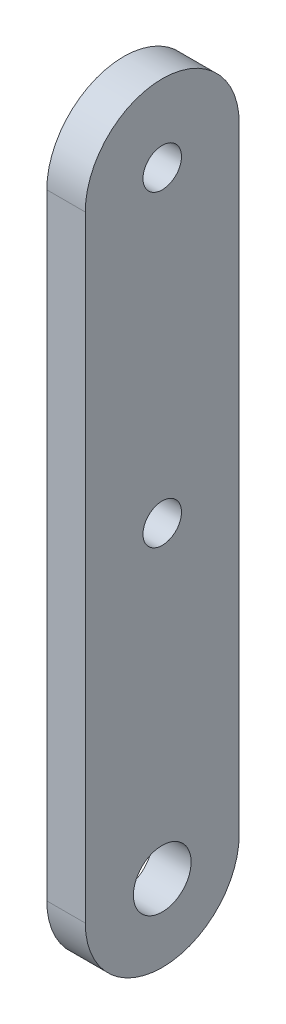
SolidWorks part; units mm, degrees
material "6061-T6 (SS)"
ref_plane "Front Plane" through (0, 0, 0) normal (0, 0, 1) x (1, 0, 0)
ref_plane "Top Plane" through (0, 0, 0) normal (0, 1, 0) x (1, 0, 0)
ref_plane "Right Plane" through (0, 0, 0) normal (1, 0, 0) x (0, 0, -1)
sketch "Sketch1" plane through (0, 0, 0) normal (1, 0, 0) x (0, 0, -1)
  line L0 (0, 50.8) -> (0, 0) construction
  line L3 (0, 0) -> (0, -50.8) construction
  line L4 (12.7, 50.8) -> (12.7, -50.8)
  line L5 (-12.7, 50.8) -> (-12.7, -50.8)
  arc A0 (12.7, 50.8) -> (-12.7, 50.8) centre (0, 50.8) ccw
  arc A3 (-12.7, -50.8) -> (12.7, -50.8) centre (0, -50.8) ccw
  circle A4 centre (0, 50.8) radius 3.175
  circle A5 centre (0, 0) radius 3.175
  circle A6 centre (0, -50.8) radius 4.7625
  point P3 (0, 15.1395)
  point P10 (0, -17.7431)
  dimension "D1" = 6.35
  dimension "D2" = 9.525
  dimension "D3" = 25.4
  dimension "D4" = 50.8
  dimension "D5" = 50.8
extrude "Boss-Extrude1" add sketch "Sketch1" along normal blind 6.35
